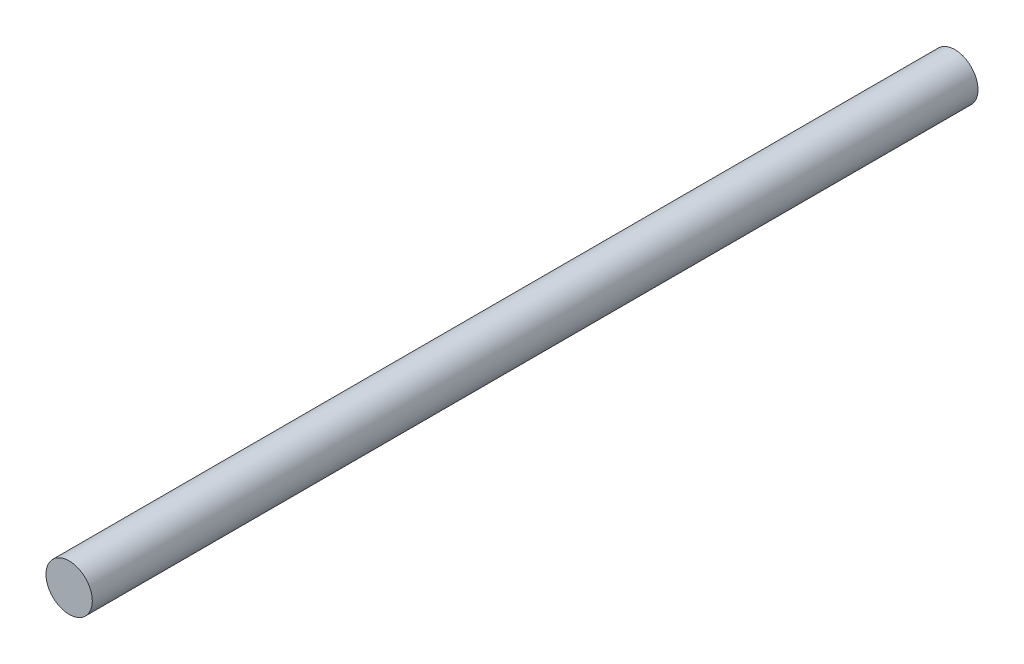
SolidWorks part; units mm, degrees
ref_plane "Front Plane" through (0, 0, 0) normal (0, 0, 1) x (1, 0, 0)
ref_plane "Top Plane" through (0, 0, 0) normal (0, 1, 0) x (1, 0, 0)
ref_plane "Right Plane" through (0, 0, 0) normal (1, 0, 0) x (0, 0, -1)
sketch "Sketch1" plane through (0, 0, 0) normal (0, 0, 1) x (1, 0, 0)
  circle A0 centre (0, 0) radius 3.9878
  dimension "D1" = 7.9756
extrude "Boss-Extrude1" add sketch "Sketch1" along normal blind 152.4 contours A0
